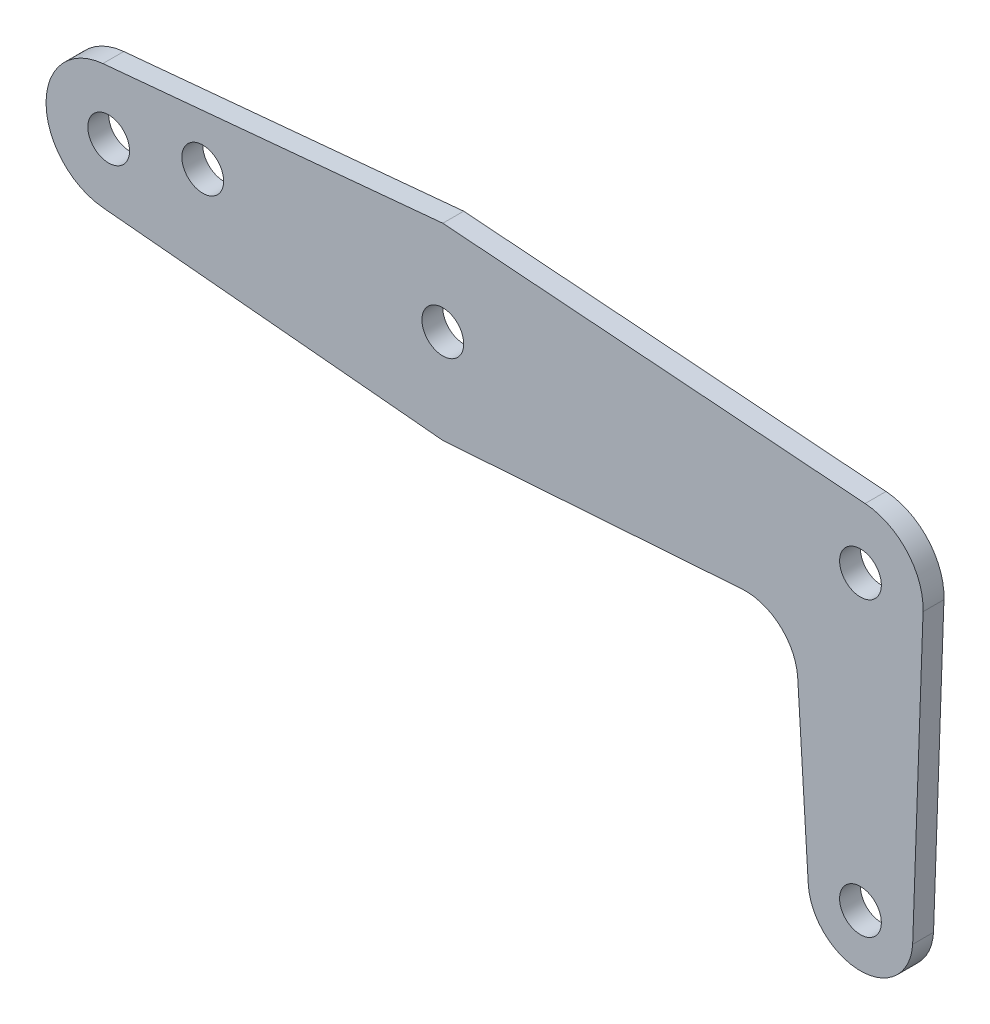
SolidWorks part; units mm, degrees
material "1023 Carbon Steel Sheet (SS)"
ref_plane "Front Plane" through (0, 0, 0) normal (0, 0, 1) x (1, 0, 0)
ref_plane "Top Plane" through (0, 0, 0) normal (0, 1, 0) x (1, 0, 0)
ref_plane "Right Plane" through (0, 0, 0) normal (1, 0, 0) x (0, 0, -1)
sketch "Sketch2" plane through (0, 0, 0) normal (0, 0, 1) x (1, 0, 0)
  line L0 (-45, 0) -> (0, 0) construction
  line L1 (0, 0) -> (0, -17.5) construction
  line L2 (0.2796, 3.7396) -> (-25, 5.63)
  line L3 (-25, 5.63) -> (-45.3479, 3.7338)
  line L4 (-25, -5.63) -> (-45.3479, -3.7338)
  line L5 (-25, 5.63) -> (-25, -5.63) construction
  line L6 (3.1242, -17.6901) -> (3.7476, -0.1331)
  line L7 (-3.1242, -17.6901) -> (-3.7558, -7.3099)
  line L8 (-7.0984, -4.3776) -> (-25, -5.63)
  arc A0 (-3.7558, -7.3099) -> (-7.0984, -4.3776) centre (-6.88, -7.5) ccw
  arc A1 (0.2796, 3.7396) -> (3.7476, -0.1331) centre (0, 0) cw
  arc A2 (-3.1242, -17.6901) -> (3.1242, -17.6901) centre (0, -17.5) ccw
  circle A3 centre (0, 0) radius 1.25
  circle A4 centre (0, -17.5) radius 1.25
  circle A5 centre (-45, 0) radius 1.25
  circle A6 centre (-25, 0) radius 1.25
  arc A7 (-45.3479, 3.7338) -> (-45.3479, -3.7338) centre (-45, 0) ccw
  circle A8 centre (-39.37, 1.25) radius 1.25
  point P9 (-25, 0)
  point P22 (0, 0)
  point P25 (0, 0)
  point P26 (0, 0)
  point P27 (-25, -5.63)
  point P28 (-45.2019, 0)
  dimension "D5" = 3.13
  dimension "D6" = 3.75
  dimension "D8" = 3.13
  dimension "D9" = 2.5
  dimension "D10" = 3.75
  dimension "D2" = 17.5
  dimension "D3" = 5.63
  dimension "D4" = 25
  dimension "D7" = 6.88
  dimension "D11" = 5.63
  dimension "D12" = 7.5
  dimension "D13" = 20
extrude "Boss-Extrude1" add sketch "Sketch2" along normal blind 1.25
